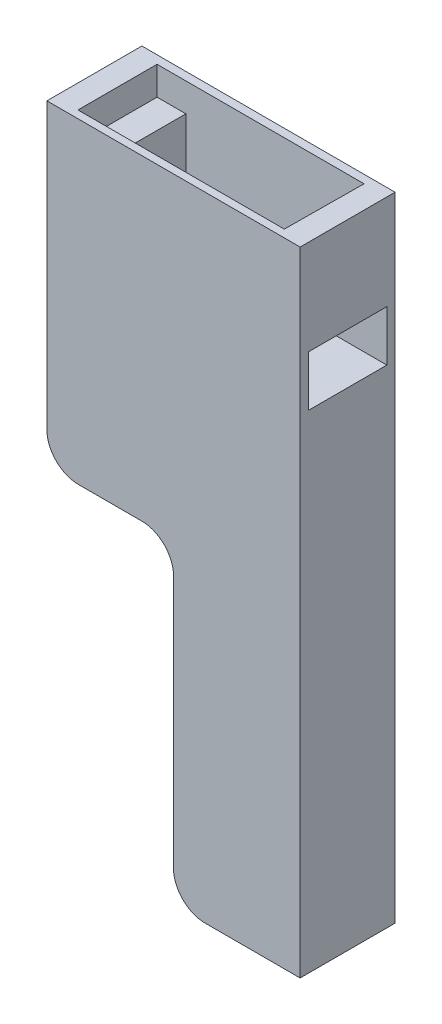
SolidWorks part; units mm, degrees
ref_plane "정면" through (0, 0, 0) normal (0, 0, 1) x (1, 0, 0)
ref_plane "윗면" through (0, 0, 0) normal (0, 1, 0) x (1, 0, 0)
ref_plane "우측면" through (0, 0, 0) normal (1, 0, 0) x (0, 0, -1)
sketch "스케치1" plane through (0, 0, 0) normal (0, 1, 0) x (1, 0, 0)
  line L0 (-51.2308, 0) -> (54.1538, 0) construction
  line L1 (0, 37.5) -> (0, -40.8077) construction
  line L3 (20, -7.5) -> (-20, -7.5)
  line L4 (20, -7.5) -> (20, 7.5)
  line L5 (20, 7.5) -> (-20, 7.5)
  line L6 (-20, -7.5) -> (-20, 7.5)
  line L7 (20, -7.5) -> (-20, 7.5) construction
  line L8 (20, 7.5) -> (-20, -7.5) construction
  point P5 (0, 0)
  dimension "D1" = 40
  dimension "D2" = 15
extrude "보스-돌출1" add sketch "스케치1" along normal mid plane 100
sketch "스케치2" plane through (0, 0, 7.5) normal (0, 0, 1) x (1, 0, 0)
  line L1 (-20, -50) -> (0, -50)
  line L2 (-20, -50) -> (-20, 0)
  line L3 (-20, 0) -> (0, 0)
  line L4 (0, -50) -> (0, 0)
  dimension "D1" = 20
  dimension "D2" = 50
extrude "컷-돌출1" cut sketch "스케치2" against normal through all
fillet "필렛2" radius 5 2 edges at (0, 0, 0) (-20, 0, 0)
fillet "필렛3" radius 5 1 edges at (0, -50, 0)
sketch "스케치4" plane through (0, 50, 0) normal (0, 1, 0) x (1, 0, 0)
  line L0 (16.4, 6.2) -> (-16.3, 6.2)
  line L5 (20, 7.5) -> (-20, 7.5) construction
  line L6 (-20, 7.5) -> (-20, -7.5) construction
  line L7 (-16.3, -6.3) -> (-16.3, 6.2)
  line L8 (16.3, -6.3) -> (-16.3, -6.3)
  line L9 (16.3, -6.3) -> (16.4, 6.2)
  line L10 (20, -7.5) -> (20, 7.5) construction
  line L12 (-20, -7.5) -> (20, -7.5) construction
  point P0 (0, 0)
  dimension "D1" = 32.7
  dimension "D2" = 12.5
  dimension "D3" = 1.3
  dimension "D4" = 3.7
  dimension "D5" = 3.7
extrude "컷-돌출2" cut sketch "스케치4" against normal blind 4.5
sketch "스케치5" plane through (0, 45.5, 0) normal (0, 1, 0) x (1, 0, 0)
  line L0 (16.4, 6.2) -> (-16.3, 6.2) construction
  line L1 (11.75, -6.2) -> (-11.75, -6.2)
  line L2 (11.75, -6.2) -> (11.75, 6.2)
  line L3 (11.75, 6.2) -> (-11.75, 6.2)
  line L4 (-11.75, -6.2) -> (-11.75, 6.2)
  line L5 (11.75, -6.2) -> (-11.75, 6.2) construction
  line L6 (11.75, 6.2) -> (-11.75, -6.2) construction
  point P0 (0, 0)
  dimension "D1" = 23.5
extrude "컷-돌출3" cut sketch "스케치5" against normal blind 18.5
sketch "스케치7" plane through (11.75, 0, 0) normal (-1, 0, 0) x (0, 0, 1)
  line L0 (6.2, 27) -> (6.2, 45.5) construction
  line L1 (-6.2, 27) -> (6.2, 27)
  line L2 (-6.2, 27) -> (-6.2, 35)
  line L3 (-6.2, 35) -> (6.2, 35)
  line L4 (6.2, 27) -> (6.2, 35)
  dimension "D1" = 8
extrude "컷-돌출4" cut sketch "스케치7" against normal through all
sketch "스케치10" plane through (0, 45.5, 0) normal (0, 1, 0) x (1, 0, 0)
  line L0 (16.4, 6.2) -> (11.75, 6.2) construction
  line L2 (13.75, 6.2) -> (13.75, -6.3)
  line L5 (11.75, -6.2) -> (11.75, 6.2) construction
  line L7 (11.75, 6.2) -> (13.75, 6.2)
  line L8 (11.75, 6.2) -> (11.75, -6.3)
  line L9 (11.75, -6.3) -> (13.75, -6.3)
  line L10 (13.75, 6.2) -> (13.75, -6.3)
  line M8 (-16.3, -6.3) -> (16.3, -6.3)
  line M10 (16.4, 6.2) -> (11.75, 6.2)
  line M11 (11.75, 6.2) -> (11.75, -6.2)
  dimension "D1" = 2
extrude "컷-돌출7" cut sketch "스케치10" against normal blind 12 contours L8 L2 M11 M8 M10
